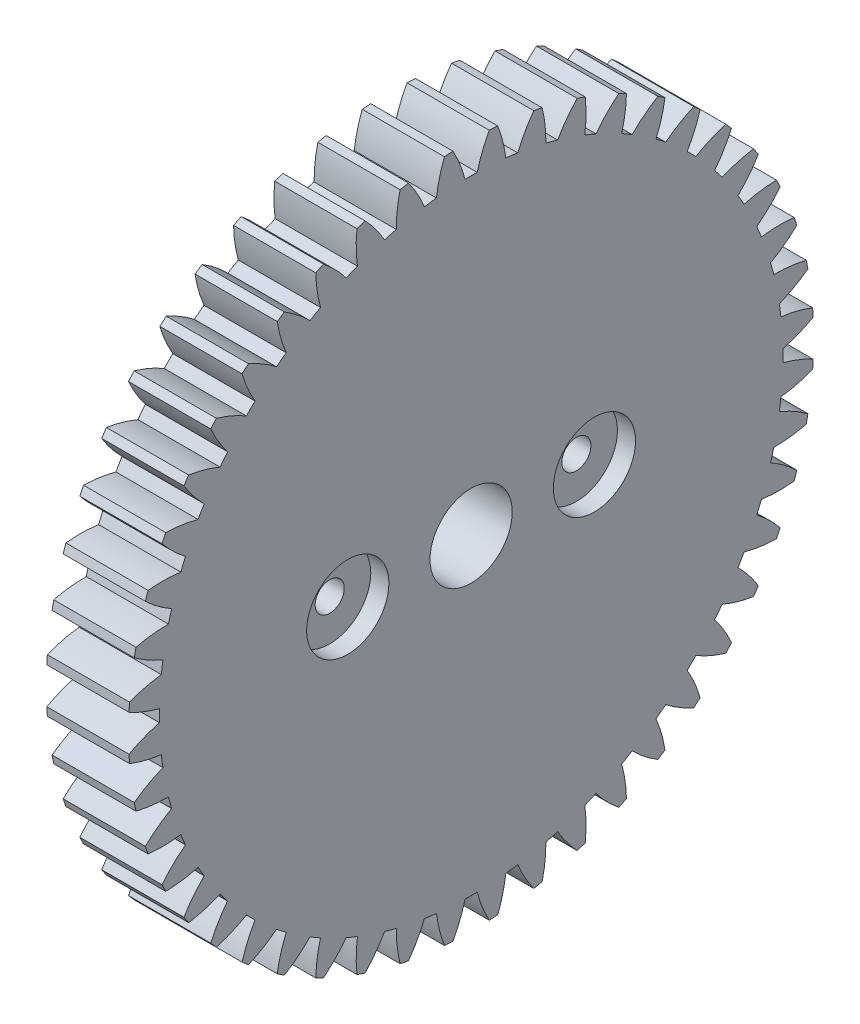
SolidWorks part; units mm, degrees
ref_plane "Plane1" through (0, 0, 0) normal (0, 0, 1) x (1, 0, 0)
ref_plane "Plane2" through (0, 0, 0) normal (0, 1, 0) x (1, 0, 0)
ref_plane "Plane3" through (0, 0, 0) normal (1, 0, 0) x (0, 0, -1)
sketch "HoldingSke" plane through (0, 0, 0) normal (0, 1, 0) x (1, 0, 0)
  line L0 (0, 0) -> (203.951, -226.5105)
  line L1 (-15, 0) -> (100, 0) construction
  line L2 (0, 0) -> (-2.1039, 2.3779)
  line L3 (0, 0) -> (-11.863, 4.5341)
  line L4 (0, 0) -> (5.7786, 6.4178)
  line L5 (0, 0) -> (-47.5972, -17.7524)
  line L6 (0, 0) -> (-10.5278, -7.1032)
  line L7 (-2.1039, 2.3779) -> (8.8308, 51.9871)
  line L8 (-76.2, 54.61) -> (-61.976, 54.61)
  line L9 (-71.009, 38.7566) -> (-53.1078, 45.2721)
  line L10 (-76.2, 71.12) -> (104.1128, 71.12)
  line L11 (0, 0) -> (-12.7, 0)
  line L12 (-76.2, 101.6) -> (-76.1147, 101.6)
  line L13 (24.9733, 27.94) -> (52.9518, 28.4284)
  line L14 (24.9733, 27.94) -> (24.9746, 27.94)
  line L15 (24.9733, 27.94) -> (100.4006, 29.5858)
  circle A0 centre (0, 0) radius 6.35
  circle A1 centre (0, 0) radius 38.1
  circle A2 centre (0, 0) radius 38.1
  circle A3 centre (0, 0) radius 6.35
  dimension "MHD" = 76.2
  dimension "Hub_dia" = 76.2
  dimension "Bore" = 12.7
  dimension "MBD" = 12.7
  dimension "Num_teeth" = 48
  dimension "Pitch" = 304.8
  dimension "Overall_len" = 50.8
  dimension "Show_teeth" = 48
  dimension "Thickness" = 12.7
  dimension "OAL" = 50.8001
  dimension "T_dim" = 14.224
  dimension "Ap" = 20
  dimension "H" = 19.05
  dimension "Pitch_radius" = 180.3128
  dimension "Width" = 12.7
  dimension "Backlash" = 0.0853
  dimension "Addendum_fac" = 1
  dimension "Dedendum_fac" = 1.25
  dimension "Clearance_fac" = 0.25
  dimension "Dedendum_add" = 0.0013
sketch "BasProSke" plane through (0, 0, 0) normal (0, 1, 0) x (1, 0, 0)
  line L0 (-10, 0) -> (60, 0) construction
  line L1 (0, 0) -> (0, 52.9167)
  line L2 (0, 0) -> (12.7, 0)
  line L3 (12.7, 0) -> (12.7, 52.9167)
  line L4 (12.7, 52.9167) -> (0, 52.9167)
  dimension "Thickness" = 12.7
  dimension "Diameter" = 105.8333
revolve "Base-Revolve" add sketch "BasProSke" angle 360 about L0
sketch "TooCutSke" plane through (0, 0, 0) normal (1, 0, 0) x (0, 0, -1)
  line L1 (0, 0) -> (0, 107) construction
  line L2 (0, 0) -> (-1.8115, 50.7677) construction
  line L3 (0, 0) -> (-6.642, 101.3375) construction
  line L4 (-1.8115, 50.7677) -> (-3.321, 50.6688) construction
  arc A0 (0.9387, 48.1437) -> (-0.9387, 48.1437) centre (0, 0) ccw
  arc A1 (2.8166, 52.8671) -> (-2.8166, 52.8671) centre (0, 0) ccw
  circle A2 centre (0, 0) radius 50.8 construction
  circle A3 centre (0, 0) radius 47.7364 construction
  arc A4 (-0.9387, 48.1437) -> (-2.8166, 52.8671) centre (-20.6117, 43.0572) ccw
  arc A5 (2.8166, 52.8671) -> (0.9387, 48.1437) centre (20.6117, 43.0572) ccw
  dimension "Root_dia" = 96.3058
  dimension "Overcut_dia" = 105.8841
  dimension "Pitch_dia" = 101.6
  dimension "Base_dia" = 95.4728
  dimension "Flank_rad" = 20.32
  dimension "Half_ang" = 3.75
  dimension "Half_CT" = 1.5128
extrude "ToothCut" cut sketch "TooCutSke" along normal through all
fillet "Breaks" [suppressed] radius 0.0423
fillet "RootFillets" [suppressed] radius 0.5304
pattern_circular "TeethCuts" count 48 every 7.5 about axis through (-10, 0, 0) along (1, 0, 0) of "ToothCut", "RootFillets", "Breaks"
sketch "HubNeaOneSke" plane through (0, 0, 0) normal (-1, 0, 0) x (0, 0, 1)
  circle A0 centre (0, 0) radius 38.1
  dimension "Diameter" = 76.2
extrude "HubNearOne" [suppressed] add sketch "HubNeaOneSke" along normal blind 38.1001
sketch "HubNeaBotSke" plane through (0, 0, 0) normal (-1, 0, 0) x (0, 0, 1)
  circle A0 centre (0, 0) radius 38.1
  dimension "Diameter" = 76.2
extrude "HubNearBoth" [suppressed] add sketch "HubNeaBotSke" along normal blind 19.05
ref_plane "FarPln" through (12.7, 0, 0) normal (1, 0, 0) x (0, 0, -1)
sketch "HubFarSke" plane through (12.7, 0, 0) normal (1, 0, 0) x (0, 0, -1)
  circle A0 centre (0, 0) radius 38.1
  dimension "Diameter" = 76.2
extrude "HubFar" [suppressed] add sketch "HubFarSke" along normal blind 19.05
sketch "BorSke" plane through (0, 0, 0) normal (1, 0, 0) x (0, 0, -1)
  circle A0 centre (0, 0) radius 6.35
  dimension "Diameter" = 12.7
extrude "Bore" cut sketch "BorSke" along normal mid plane 101.6001
sketch "KeySke" plane through (0, 0, 0) normal (1, 0, 0) x (0, 0, -1)
  line L0 (-1.5875, 0) -> (-1.5875, 7.874)
  line L1 (-1.5875, 7.874) -> (1.5875, 7.874)
  line L2 (1.5875, 7.874) -> (1.5875, 0)
  line L3 (0, 0) -> (0, 34) construction
  line L4 (-1.5875, 0) -> (1.5875, 0)
  dimension "Offset" = 7.874
  dimension "Width" = 3.175
extrude "Keyway" [suppressed] cut sketch "KeySke" along normal mid plane 101.6001
pattern_circular "Keyway2" [suppressed] count 2 every 90 about axis through (-10, 0, 0) along (1, 0, 0)
sketch "Sketch1" plane through (12.7, 0, 0) normal (1, 0, 0) x (0, 0, -1)
  line L0 (28.7127, 0) -> (-34.3854, 0) construction
  line L1 (0, 22.8901) -> (0, -21.3069) construction
hole_wizard "CBORE for #8 Hex Machine Screw2" positions "Sketch6" profile "Sketch7" counterbore size "#8" standard "ANSI Inch" end condition through all
sketch "Sketch6" plane through (12.7, 0, 0) normal (1, 0, 0) x (0, 0, -1)
  line L0 (0, 22.8901) -> (0, -21.3069) construction
  line L2 (28.7127, 0) -> (-34.3854, 0) construction
  point P0 (19.05, 0)
  point P14 (-19.05, 0)
  point P17 (-19.05, 6.132)
  point P18 (0, 0)
  dimension "D1" = 19.05
  dimension "D2" = 19.05
sketch "Sketch7" plane through (12.7, 0, -19.05) normal (0, 1, 0) x (0, 0, -1)
  line L0 (0, 0) -> (0, 12.7)
  line L1 (0, 12.7) -> (2.2479, 12.7)
  line L3 (2.2479, 12.7) -> (2.2479, 2.794)
  line L4 (2.2479, 2.794) -> (6.35, 2.794)
  line L5 (6.35, 2.794) -> (6.35, 0)
  line L7 (6.35, 0) -> (0, 0)
  line L11 (0, -6.35) -> (0, 107.95) construction
  dimension "Thru Hole Dia." = 4.4958
  dimension "Thru Hole Depth" = 12.7
  dimension "C'Bore Dia." = 12.7
  dimension "C'Bore Depth" = 2.794
equation "' \"Pitch@HoldingSke\" = 4"
equation "' \"Num_teeth@HoldingSke\" = 12"
equation "' \"Ap@HoldingSke\" =  20"
equation "' \"Ap@HoldingSke\" = 20"
equation "' \"Width@HoldingSke\" = 0.5"
equation "' \"Hub_dia@HoldingSke\"= 1"
equation "' \"Hub_dia@HoldingSke\" = 1"
equation "' \"Overall_len@HoldingSke\" = 1.0"
equation "' \"Bore@HoldingSke\" = 0.75"
equation "' \"T_dim@HoldingSke\" = 0.85"
equation "' \"Width@KeySke\" = 0.25"
equation "' \"Show_teeth@HoldingSke\" = 13"
equation "' \"Backlash@HoldingSke\" = 0.009"
equation "' \"Addendum_fac@HoldingSke\" = 1.0"
equation "' \"Dedendum_fac@HoldingSke\" = 1.25"
equation "' \"Dedendum_add@HoldingSke\" = 0.00005"
equation "' \"Clearance_fac@HoldingSke\" = 0.25"
equation "' \"Pitch@HoldingSke\" = 0.5"
equation "' \"Num_teeth@HoldingSke\" = 23"
equation "' \"Show_teeth@HoldingSke\" = 23"
equation "' \"Backlash@HoldingSke\" = 0.0375"
equation "\"Overcut_dia@TooCutSke\" = (\"Num_teeth@HoldingSke\" + 2 * \"Addendum_fac@HoldingSke\") / \"Pitch@HoldingSke\" + 0.002"
equation "\"Pitch_dia@TooCutSke\" = \"Num_teeth@HoldingSke\" / \"Pitch@HoldingSke\""
equation "\"Base_dia@TooCutSke\" = \"Num_teeth@HoldingSke\" / \"Pitch@HoldingSke\" * cos((\"Ap@HoldingSke\"  * 3.14159265 / 180))"
equation "\"Root_dia@TooCutSke\" = (\"Num_teeth@HoldingSke\" + 2) / \"Pitch@HoldingSke\" - 2 * (\"Addendum_fac@HoldingSke\" + \"Dedendum_fac@HoldingSke\") / \"Pitch@HoldingSke\" - \"Dedendum_add@HoldingSke\" * 2"
equation "\"Half_ang@TooCutSke\" = 180 / \"Num_teeth@HoldingSke\""
equation "\"Half_CT@TooCutSke\" = \"Num_teeth@HoldingSke\" / \"Pitch@HoldingSke\" * sin((3.14159265 / 2 / \"Num_teeth@HoldingSke\")) / 2 - 7 * \"Backlash@HoldingSke\" / 4"
equation "\"Flank_rad@TooCutSke\" = \"Num_teeth@HoldingSke\" / \"Pitch@HoldingSke\" / 5"
equation "\"Radius@RootFillets\" = \"Clearance_fac@HoldingSke\" / \"Pitch@HoldingSke\" + \"Dedendum_add@HoldingSke\""
equation "\"Break_rad@Breaks\" = 0.02 / \"Pitch@HoldingSke\""
equation "\"Thickness@HoldingSke\" = \"Width@HoldingSke\""
equation "\"OAL@HoldingSke\" = \"Thickness@HoldingSke\""
equation "\"MHD@HoldingSke\" = (\"Num_teeth@HoldingSke\" + 2) / \"Pitch@HoldingSke\" - 2 * (\"Addendum_fac@HoldingSke\" + \"Dedendum_fac@HoldingSke\")  / \"Pitch@HoldingSke\" - \"Dedendum_add@HoldingSke\" * 2"
equation "\"MBD@HoldingSke\" = (\"Num_teeth@HoldingSke\" + 2) / \"Pitch@HoldingSke\" - 2 * (\"Addendum_fac@HoldingSke\" + \"Dedendum_fac@HoldingSke\")  / \"Pitch@HoldingSke\" - \"Dedendum_add@HoldingSke\" * 2 - 0.002"
equation "\"MHD@HoldingSke\" = ((sgn( \"MHD@HoldingSke\" - \"Hub_dia@HoldingSke\" )-1)*( \"MHD@HoldingSke\" - \"Hub_dia@HoldingSke\" ))/-2+ \"Hub_dia@HoldingSke\""
equation "\"MBD@HoldingSke\" = ((sgn( \"MBD@HoldingSke\" - \"Bore@HoldingSke\" )-1)*( \"MBD@HoldingSke\" - \"Bore@HoldingSke\" ))/-2+ \"Bore@HoldingSke\""
equation "\"OAL@HoldingSke\" = ((sgn( \"OAL@HoldingSke\" - \"Overall_len@HoldingSke\" )+1)*( \"OAL@HoldingSke\" - \"Overall_len@HoldingSke\" ))/2 + \"Overall_len@HoldingSke\" + 0.000002"
equation "\"Num_teeth@TeethCuts\" = int( \"Show_teeth@HoldingSke\" ) + 1"
equation "\"Num_teeth@TeethCuts\" = ((sgn( \"Num_teeth@TeethCuts\" - \"Num_teeth@HoldingSke\" )-1)*( \"Num_teeth@TeethCuts\" - \"Num_teeth@HoldingSke\" ))/-2+ \"Num_teeth@HoldingSke\""
equation "\"Num_teeth@TeethCuts\" = ((sgn( \"Num_teeth@TeethCuts\" - 2.0)+1)*( \"Num_teeth@TeethCuts\" - 2.0))/2 +2.0"
equation "\"Angle@TeethCuts\" = 360.0 / \"Num_teeth@HoldingSke\""
equation "\"Diameter@BasProSke\" = (\"Num_teeth@HoldingSke\" + 2 * \"Addendum_fac@HoldingSke\") / \"Pitch@HoldingSke\""
equation "\"Thickness@BasProSke\"  = \"Thickness@HoldingSke\""
equation "' \"Fillet_rad@BasProSke\" =  \"Thickness@HoldingSke\" * 0.05"
equation "' \"Fillet_rad@BasProSke\" = \"Thickness@HoldingSke\" * 0.05"
equation "\"MHD@HoldingSke\" = ((sgn( \"MHD@HoldingSke\" - \"Root_dia@TooCutSke\" )-1)*( \"MHD@HoldingSke\" - \"Root_dia@TooCutSke\" ))/-2+ \"Root_dia@TooCutSke\""
equation "\"Diameter@HubNeaOneSke\" = \"MHD@HoldingSke\""
equation "\"Length@HubNearOne\" = \"OAL@HoldingSke\" - \"Thickness@BasProSke\""
equation "\"Diameter@HubNeaBotSke\" = \"MHD@HoldingSke\""
equation "\"Length@HubNearBoth\" = ( \"OAL@HoldingSke\" - \"Thickness@BasProSke\" ) / 2.0"
equation "\"Thickness@FarPln\" = \"Thickness@BasProSke\""
equation "\"Diameter@HubFarSke\" = \"MHD@HoldingSke\""
equation "\"Length@HubFar\" = ( \"OAL@HoldingSke\" - \"Thickness@BasProSke\" ) / 2.0"
equation "\"Diameter@BorSke\" = \"MBD@HoldingSke\""
equation "\"D1@Bore\" = \"OAL@HoldingSke\" * 2.0"
equation "\"D1@Keyway\" = \"OAL@HoldingSke\" * 2.0"
equation "\"Offset@KeySke\" = \"T_dim@HoldingSke\" - \"MBD@HoldingSke\" / 2.0"
